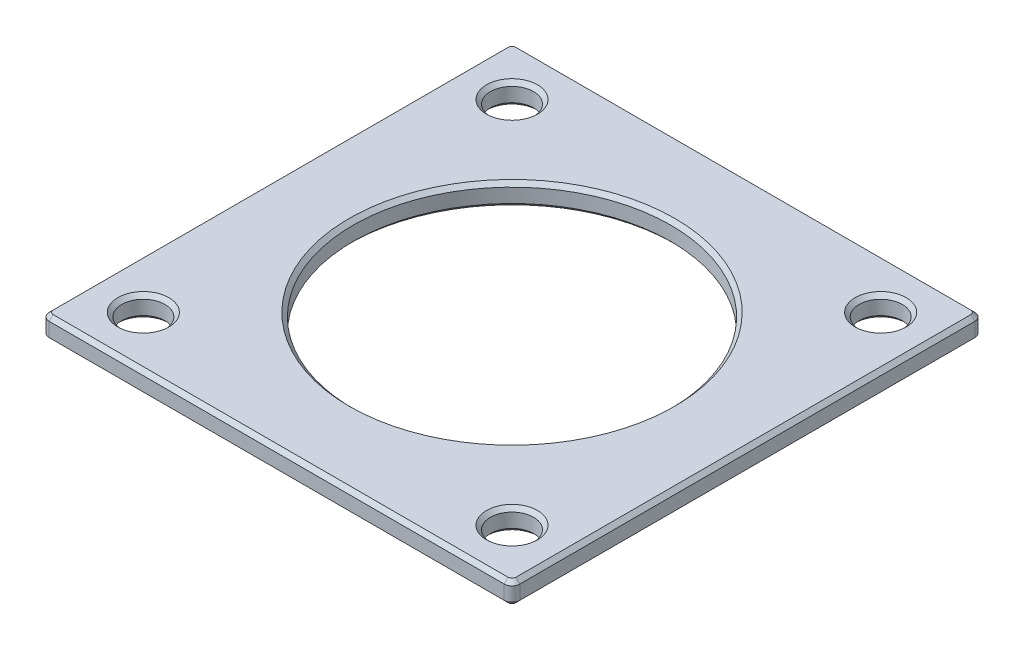
SolidWorks part; units mm, degrees
ref_plane "Front Plane" through (0, 0, 0) normal (0, 0, 1) x (1, 0, 0)
ref_plane "Top Plane" through (0, 0, 0) normal (0, 1, 0) x (1, 0, 0)
ref_plane "Right Plane" through (0, 0, 0) normal (1, 0, 0) x (0, 0, -1)
sketch "Sketch1" plane through (0, 0, 0) normal (0, 1, 0) x (1, 0, 0)
  line L7 (-2.3976, -65.4871) -> (-60.3976, -65.4871)
  line L8 (-1.3976, -64.4871) -> (-1.3976, -6.4871)
  line L9 (-2.3976, -5.4871) -> (-60.3976, -5.4871)
  line L10 (-61.3976, -64.4871) -> (-61.3976, -6.4871)
  line L11 (-1.3976, -65.4871) -> (-61.3976, -5.4871) construction
  line L12 (-1.3976, -5.4871) -> (-61.3976, -65.4871) construction
  circle A0 centre (-31.3976, -35.4871) radius 20.25
  circle A1 centre (-54.8976, -11.9871) radius 2.75
  circle A2 centre (-7.8976, -11.9871) radius 2.75
  circle A3 centre (-7.8976, -58.9871) radius 2.75
  circle A4 centre (-54.8976, -58.9871) radius 2.75
  arc A5 (-60.3976, -65.4871) -> (-61.3976, -64.4871) centre (-60.3976, -64.4871) cw
  arc A6 (-2.3976, -65.4871) -> (-1.3976, -64.4871) centre (-2.3976, -64.4871) ccw
  arc A7 (-1.3976, -6.4871) -> (-2.3976, -5.4871) centre (-2.3976, -6.4871) ccw
  arc A8 (-60.3976, -5.4871) -> (-61.3976, -6.4871) centre (-60.3976, -6.4871) ccw
  point P0 (0, 0)
  point P1 (-7.8976, -58.9871)
  point P2 (0, 0)
  point P5 (-20.2708, -32.2779)
  point P10 (-21.7072, -31.1738)
  point P21 (-31.3976, -35.4871)
  point P22 (0, 0)
  point P23 (11.0487, -2.6925)
  point P24 (0, 0)
  dimension "D1" = 5.5
  dimension "D2" = 40.5
  dimension "D6" = 1
  dimension "D3" = 60
  dimension "D5" = 47
  dimension "D4" = 4
extrude "Boss-Extrude1" add sketch "Sketch1" along normal blind 2.8
chamfer "Chamfer1" distance 0.5 angle 45 26 edges at (-54.8976, 0, 61.7371) (-7.8976, 0, 14.7371) (-31.3976, 0, 55.7371) (-31.3976, 0, 65.4871) (-1.6905, 0, 65.1942) (-1.3976, 0, 35.4871) (-1.6905, 0, 5.78) (-31.3976, 0, 5.4871) (-61.1047, 0, 5.78) (-61.3976, 0, 35.4871) (-61.1047, 0, 65.1942) (-54.8976, 0, 14.7371) (-7.8976, 0, 61.7371) (-54.8976, 2.8, 61.7371) (-7.8976, 2.8, 61.7371) (-7.8976, 2.8, 14.7371) (-54.8976, 2.8, 14.7371) (-31.3976, 2.8, 55.7371) (-61.3976, 2.8, 35.4871) (-61.1047, 2.8, 5.78) (-31.3976, 2.8, 5.4871) (-1.6905, 2.8, 5.78) (-1.3976, 2.8, 35.4871) (-1.6905, 2.8, 65.1942) (-31.3976, 2.8, 65.4871) (-61.1047, 2.8, 65.1942)
